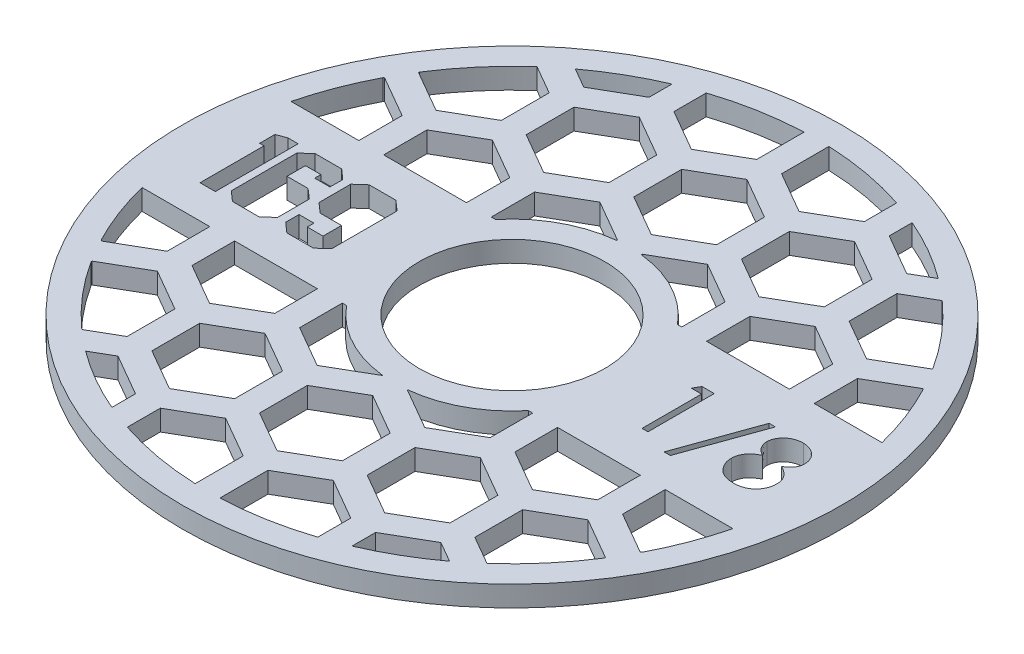
SolidWorks part; units mm, degrees
ref_plane "Front Plane" through (0, 0, 0) normal (0, 0, 1) x (1, 0, 0)
ref_plane "Top Plane" through (0, 0, 0) normal (0, 1, 0) x (1, 0, 0)
ref_plane "Right Plane" through (0, 0, 0) normal (1, 0, 0) x (0, 0, -1)
sketch "Sketch1" plane through (0, 0, 0) normal (0, 1, 0) x (1, 0, 0)
  circle A0 centre (0, 0) radius 14.224
  circle A1 centre (0, 0) radius 50.546
  dimension "D1" = 28.448
  dimension "D2" = 101.092
extrude "Boss-Extrude1" add sketch "Sketch1" along normal blind 3.175
sketch "Sketch2" plane through (0, 3.175, 0) normal (0, 1, 0) x (1, 0, 0)
  line L0 (-14.224, 0) -> (-50.546, 0) construction
  line L1 (-14.224, -6.35) -> (-50.546, -6.35) construction
  line L2 (14.224, 0) -> (50.546, 0) construction
  line L3 (14.224, -5.08) -> (50.546, -5.08) construction
  circle A0 centre (0, 0) radius 14.224 construction
  circle A1 centre (0, 0) radius 50.546 construction
  text T0 "169" font "Jersey M54" height 12.7
  text T1 "1/8" font "Century Gothic" height 10.16
  dimension "D1" = 6.35
  dimension "D2" = 5.08
extrude "Cut-Extrude1" cut sketch "Sketch2" against normal through all both and the other way through all
sketch "Sketch3" plane through (0, 3.175, 0) normal (0, 1, 0) x (1, 0, 0)
  line L0 (0, 11.43) -> (0, -11.43)
  line L1 (-49.2367, 11.43) -> (49.2367, 11.43)
  line L2 (-49.2367, -11.43) -> (49.2367, -11.43)
  line L3 (16.51, -7.3323) -> (22.86, -3.6662)
  line L4 (0, -7.3323) -> (6.35, -3.6662)
  line L5 (6.35, -3.6662) -> (6.35, 3.6662)
  line L6 (6.35, 3.6662) -> (0, 7.3323)
  line L7 (0, 7.3323) -> (-6.35, 3.6662)
  line L8 (-6.35, 3.6662) -> (-6.35, -3.6662)
  line L9 (-6.35, -3.6662) -> (0, -7.3323)
  line L16 (8.255, -21.6304) -> (14.605, -17.9643)
  line L17 (14.605, -17.9643) -> (14.605, -10.6319)
  line L18 (14.605, -10.6319) -> (8.255, -6.9657)
  line L19 (8.255, -6.9657) -> (1.905, -10.6319)
  line L20 (1.905, -10.6319) -> (1.905, -17.9643)
  line L21 (1.905, -17.9643) -> (8.255, -21.6304)
  line L22 (22.86, -3.6662) -> (22.86, 3.6662)
  line L23 (22.86, 3.6662) -> (16.51, 7.3323)
  line L24 (16.51, 7.3323) -> (10.16, 3.6662)
  line L25 (10.16, 3.6662) -> (10.16, -3.6662)
  line L26 (10.16, -3.6662) -> (16.51, -7.3323)
  line L27 (24.765, -21.6304) -> (31.115, -17.9643)
  line L28 (31.115, -17.9643) -> (31.115, -10.6319)
  line L29 (31.115, -10.6319) -> (24.765, -6.9657)
  line L30 (24.765, -6.9657) -> (18.415, -10.6319)
  line L31 (18.415, -10.6319) -> (18.415, -17.9643)
  line L32 (18.415, -17.9643) -> (24.765, -21.6304)
  line L33 (33.02, -7.3323) -> (39.37, -3.6662)
  line L34 (39.37, -3.6662) -> (39.37, 3.6662)
  line L35 (39.37, 3.6662) -> (33.02, 7.3323)
  line L36 (33.02, 7.3323) -> (26.67, 3.6662)
  line L37 (26.67, 3.6662) -> (26.67, -3.6662)
  line L38 (26.67, -3.6662) -> (33.02, -7.3323)
  line L39 (41.275, -21.6304) -> (47.625, -17.9643)
  line L40 (47.625, -17.9643) -> (47.625, -10.6319)
  line L41 (47.625, -10.6319) -> (41.275, -6.9657)
  line L42 (41.275, -6.9657) -> (34.925, -10.6319)
  line L43 (34.925, -10.6319) -> (34.925, -17.9643)
  line L44 (34.925, -17.9643) -> (41.275, -21.6304)
  line L45 (49.53, -7.3323) -> (55.88, -3.6662)
  line L46 (55.88, -3.6662) -> (55.88, 3.6662)
  line L47 (55.88, 3.6662) -> (49.53, 7.3323)
  line L48 (49.53, 7.3323) -> (43.18, 3.6662)
  line L49 (43.18, 3.6662) -> (43.18, -3.6662)
  line L50 (43.18, -3.6662) -> (49.53, -7.3323)
  line L51 (57.785, -21.6304) -> (64.135, -17.9643)
  line L52 (64.135, -17.9643) -> (64.135, -10.6319)
  line L53 (64.135, -10.6319) -> (57.785, -6.9657)
  line L54 (57.785, -6.9657) -> (51.435, -10.6319)
  line L55 (51.435, -10.6319) -> (51.435, -17.9643)
  line L56 (51.435, -17.9643) -> (57.785, -21.6304)
  line L57 (-16.51, -7.3323) -> (-10.16, -3.6662)
  line L58 (-10.16, -3.6662) -> (-10.16, 3.6662)
  line L59 (-10.16, 3.6662) -> (-16.51, 7.3323)
  line L60 (-16.51, 7.3323) -> (-22.86, 3.6662)
  line L61 (-22.86, 3.6662) -> (-22.86, -3.6662)
  line L62 (-22.86, -3.6662) -> (-16.51, -7.3323)
  line L63 (-8.255, -21.6304) -> (-1.905, -17.9643)
  line L64 (-1.905, -17.9643) -> (-1.905, -10.6319)
  line L65 (-1.905, -10.6319) -> (-8.255, -6.9657)
  line L66 (-8.255, -6.9657) -> (-14.605, -10.6319)
  line L67 (-14.605, -10.6319) -> (-14.605, -17.9643)
  line L68 (-14.605, -17.9643) -> (-8.255, -21.6304)
  line L69 (-33.02, -7.3323) -> (-26.67, -3.6662)
  line L70 (-26.67, -3.6662) -> (-26.67, 3.6662)
  line L71 (-26.67, 3.6662) -> (-33.02, 7.3323)
  line L72 (-33.02, 7.3323) -> (-39.37, 3.6662)
  line L73 (-39.37, 3.6662) -> (-39.37, -3.6662)
  line L74 (-39.37, -3.6662) -> (-33.02, -7.3323)
  line L75 (-24.765, -21.6304) -> (-18.415, -17.9643)
  line L76 (-18.415, -17.9643) -> (-18.415, -10.6319)
  line L77 (-18.415, -10.6319) -> (-24.765, -6.9657)
  line L78 (-24.765, -6.9657) -> (-31.115, -10.6319)
  line L79 (-31.115, -10.6319) -> (-31.115, -17.9643)
  line L80 (-31.115, -17.9643) -> (-24.765, -21.6304)
  line L81 (-49.53, -7.3323) -> (-43.18, -3.6662)
  line L82 (-43.18, -3.6662) -> (-43.18, 3.6662)
  line L83 (-43.18, 3.6662) -> (-49.53, 7.3323)
  line L84 (-49.53, 7.3323) -> (-55.88, 3.6662)
  line L85 (-55.88, 3.6662) -> (-55.88, -3.6662)
  line L86 (-55.88, -3.6662) -> (-49.53, -7.3323)
  line L87 (-41.275, -21.6304) -> (-34.925, -17.9643)
  line L88 (-34.925, -17.9643) -> (-34.925, -10.6319)
  line L89 (-34.925, -10.6319) -> (-41.275, -6.9657)
  line L90 (-41.275, -6.9657) -> (-47.625, -10.6319)
  line L91 (-47.625, -10.6319) -> (-47.625, -17.9643)
  line L92 (-47.625, -17.9643) -> (-41.275, -21.6304)
  line L93 (-49.53, 21.3697) -> (-43.18, 25.0358)
  line L94 (-43.18, 25.0358) -> (-43.18, 32.3682)
  line L95 (-43.18, 32.3682) -> (-49.53, 36.0343)
  line L96 (-49.53, 36.0343) -> (-55.88, 32.3682)
  line L97 (-55.88, 32.3682) -> (-55.88, 25.0358)
  line L98 (-55.88, 25.0358) -> (-49.53, 21.3697)
  line L99 (-41.275, 7.0716) -> (-34.925, 10.7377)
  line L100 (-34.925, 10.7377) -> (-34.925, 18.0701)
  line L101 (-34.925, 18.0701) -> (-41.275, 21.7363)
  line L102 (-41.275, 21.7363) -> (-47.625, 18.0701)
  line L103 (-47.625, 18.0701) -> (-47.625, 10.7377)
  line L104 (-47.625, 10.7377) -> (-41.275, 7.0716)
  line L105 (-33.02, 21.3697) -> (-26.67, 25.0358)
  line L106 (-26.67, 25.0358) -> (-26.67, 32.3682)
  line L107 (-26.67, 32.3682) -> (-33.02, 36.0343)
  line L108 (-33.02, 36.0343) -> (-39.37, 32.3682)
  line L109 (-39.37, 32.3682) -> (-39.37, 25.0358)
  line L110 (-39.37, 25.0358) -> (-33.02, 21.3697)
  line L111 (-24.765, 7.0716) -> (-18.415, 10.7377)
  line L112 (-18.415, 10.7377) -> (-18.415, 18.0701)
  line L113 (-18.415, 18.0701) -> (-24.765, 21.7363)
  line L114 (-24.765, 21.7363) -> (-31.115, 18.0701)
  line L115 (-31.115, 18.0701) -> (-31.115, 10.7377)
  line L116 (-31.115, 10.7377) -> (-24.765, 7.0716)
  line L117 (-16.51, 21.3697) -> (-10.16, 25.0358)
  line L118 (-10.16, 25.0358) -> (-10.16, 32.3682)
  line L119 (-10.16, 32.3682) -> (-16.51, 36.0343)
  line L120 (-16.51, 36.0343) -> (-22.86, 32.3682)
  line L121 (-22.86, 32.3682) -> (-22.86, 25.0358)
  line L122 (-22.86, 25.0358) -> (-16.51, 21.3697)
  line L123 (-8.255, 7.0716) -> (-1.905, 10.7377)
  line L124 (-1.905, 10.7377) -> (-1.905, 18.0701)
  line L125 (-1.905, 18.0701) -> (-8.255, 21.7363)
  line L126 (-8.255, 21.7363) -> (-14.605, 18.0701)
  line L127 (-14.605, 18.0701) -> (-14.605, 10.7377)
  line L128 (-14.605, 10.7377) -> (-8.255, 7.0716)
  line L129 (0, 21.3697) -> (6.35, 25.0358)
  line L130 (6.35, 25.0358) -> (6.35, 32.3682)
  line L131 (6.35, 32.3682) -> (0, 36.0343)
  line L132 (0, 36.0343) -> (-6.35, 32.3682)
  line L133 (-6.35, 32.3682) -> (-6.35, 25.0358)
  line L134 (-6.35, 25.0358) -> (0, 21.3697)
  line L135 (8.255, 7.0716) -> (14.605, 10.7377)
  line L136 (14.605, 10.7377) -> (14.605, 18.0701)
  line L137 (14.605, 18.0701) -> (8.255, 21.7363)
  line L138 (8.255, 21.7363) -> (1.905, 18.0701)
  line L139 (1.905, 18.0701) -> (1.905, 10.7377)
  line L140 (1.905, 10.7377) -> (8.255, 7.0716)
  line L141 (16.51, 21.3697) -> (22.86, 25.0358)
  line L142 (22.86, 25.0358) -> (22.86, 32.3682)
  line L143 (22.86, 32.3682) -> (16.51, 36.0343)
  line L144 (16.51, 36.0343) -> (10.16, 32.3682)
  line L145 (10.16, 32.3682) -> (10.16, 25.0358)
  line L146 (10.16, 25.0358) -> (16.51, 21.3697)
  line L147 (24.765, 7.0716) -> (31.115, 10.7377)
  line L148 (31.115, 10.7377) -> (31.115, 18.0701)
  line L149 (31.115, 18.0701) -> (24.765, 21.7363)
  line L150 (24.765, 21.7363) -> (18.415, 18.0701)
  line L151 (18.415, 18.0701) -> (18.415, 10.7377)
  line L152 (18.415, 10.7377) -> (24.765, 7.0716)
  line L153 (33.02, 21.3697) -> (39.37, 25.0358)
  line L154 (39.37, 25.0358) -> (39.37, 32.3682)
  line L155 (39.37, 32.3682) -> (33.02, 36.0343)
  line L156 (33.02, 36.0343) -> (26.67, 32.3682)
  line L157 (26.67, 32.3682) -> (26.67, 25.0358)
  line L158 (26.67, 25.0358) -> (33.02, 21.3697)
  line L159 (41.275, 7.0716) -> (47.625, 10.7377)
  line L160 (47.625, 10.7377) -> (47.625, 18.0701)
  line L161 (47.625, 18.0701) -> (41.275, 21.7363)
  line L162 (41.275, 21.7363) -> (34.925, 18.0701)
  line L163 (34.925, 18.0701) -> (34.925, 10.7377)
  line L164 (34.925, 10.7377) -> (41.275, 7.0716)
  line L165 (49.53, 21.3697) -> (55.88, 25.0358)
  line L166 (55.88, 25.0358) -> (55.88, 32.3682)
  line L167 (55.88, 32.3682) -> (49.53, 36.0343)
  line L168 (49.53, 36.0343) -> (43.18, 32.3682)
  line L169 (43.18, 32.3682) -> (43.18, 25.0358)
  line L170 (43.18, 25.0358) -> (49.53, 21.3697)
  line L171 (57.785, 7.0716) -> (64.135, 10.7377)
  line L172 (64.135, 10.7377) -> (64.135, 18.0701)
  line L173 (64.135, 18.0701) -> (57.785, 21.7363)
  line L174 (57.785, 21.7363) -> (51.435, 18.0701)
  line L175 (51.435, 18.0701) -> (51.435, 10.7377)
  line L176 (51.435, 10.7377) -> (57.785, 7.0716)
  line L177 (-49.53, 50.0717) -> (-43.18, 53.7378)
  line L178 (-43.18, 53.7378) -> (-43.18, 61.0702)
  line L179 (-43.18, 61.0702) -> (-49.53, 64.7363)
  line L180 (-49.53, 64.7363) -> (-55.88, 61.0702)
  line L181 (-55.88, 61.0702) -> (-55.88, 53.7378)
  line L182 (-55.88, 53.7378) -> (-49.53, 50.0717)
  line L183 (-41.275, 35.7736) -> (-34.925, 39.4397)
  line L184 (-34.925, 39.4397) -> (-34.925, 46.7721)
  line L185 (-34.925, 46.7721) -> (-41.275, 50.4383)
  line L186 (-41.275, 50.4383) -> (-47.625, 46.7721)
  line L187 (-47.625, 46.7721) -> (-47.625, 39.4397)
  line L188 (-47.625, 39.4397) -> (-41.275, 35.7736)
  line L189 (-33.02, 50.0717) -> (-26.67, 53.7378)
  line L190 (-26.67, 53.7378) -> (-26.67, 61.0702)
  line L191 (-26.67, 61.0702) -> (-33.02, 64.7363)
  line L192 (-33.02, 64.7363) -> (-39.37, 61.0702)
  line L193 (-39.37, 61.0702) -> (-39.37, 53.7378)
  line L194 (-39.37, 53.7378) -> (-33.02, 50.0717)
  line L195 (-24.765, 35.7736) -> (-18.415, 39.4397)
  line L196 (-18.415, 39.4397) -> (-18.415, 46.7721)
  line L197 (-18.415, 46.7721) -> (-24.765, 50.4383)
  line L198 (-24.765, 50.4383) -> (-31.115, 46.7721)
  line L199 (-31.115, 46.7721) -> (-31.115, 39.4397)
  line L200 (-31.115, 39.4397) -> (-24.765, 35.7736)
  line L201 (-16.51, 50.0717) -> (-10.16, 53.7378)
  line L202 (-10.16, 53.7378) -> (-10.16, 61.0702)
  line L203 (-10.16, 61.0702) -> (-16.51, 64.7363)
  line L204 (-16.51, 64.7363) -> (-22.86, 61.0702)
  line L205 (-22.86, 61.0702) -> (-22.86, 53.7378)
  line L206 (-22.86, 53.7378) -> (-16.51, 50.0717)
  line L207 (-8.255, 35.7736) -> (-1.905, 39.4397)
  line L208 (-1.905, 39.4397) -> (-1.905, 46.7721)
  line L209 (-1.905, 46.7721) -> (-8.255, 50.4383)
  line L210 (-8.255, 50.4383) -> (-14.605, 46.7721)
  line L211 (-14.605, 46.7721) -> (-14.605, 39.4397)
  line L212 (-14.605, 39.4397) -> (-8.255, 35.7736)
  line L213 (0, 50.0717) -> (6.35, 53.7378)
  line L214 (6.35, 53.7378) -> (6.35, 61.0702)
  line L215 (6.35, 61.0702) -> (0, 64.7363)
  line L216 (0, 64.7363) -> (-6.35, 61.0702)
  line L217 (-6.35, 61.0702) -> (-6.35, 53.7378)
  line L218 (-6.35, 53.7378) -> (0, 50.0717)
  line L219 (8.255, 35.7736) -> (14.605, 39.4397)
  line L220 (14.605, 39.4397) -> (14.605, 46.7721)
  line L221 (14.605, 46.7721) -> (8.255, 50.4383)
  line L222 (8.255, 50.4383) -> (1.905, 46.7721)
  line L223 (1.905, 46.7721) -> (1.905, 39.4397)
  line L224 (1.905, 39.4397) -> (8.255, 35.7736)
  line L225 (16.51, 50.0717) -> (22.86, 53.7378)
  line L226 (22.86, 53.7378) -> (22.86, 61.0702)
  line L227 (22.86, 61.0702) -> (16.51, 64.7363)
  line L228 (16.51, 64.7363) -> (10.16, 61.0702)
  line L229 (10.16, 61.0702) -> (10.16, 53.7378)
  line L230 (10.16, 53.7378) -> (16.51, 50.0717)
  line L231 (24.765, 35.7736) -> (31.115, 39.4397)
  line L232 (31.115, 39.4397) -> (31.115, 46.7721)
  line L233 (31.115, 46.7721) -> (24.765, 50.4383)
  line L234 (24.765, 50.4383) -> (18.415, 46.7721)
  line L235 (18.415, 46.7721) -> (18.415, 39.4397)
  line L236 (18.415, 39.4397) -> (24.765, 35.7736)
  line L237 (33.02, 50.0717) -> (39.37, 53.7378)
  line L238 (39.37, 53.7378) -> (39.37, 61.0702)
  line L239 (39.37, 61.0702) -> (33.02, 64.7363)
  line L240 (33.02, 64.7363) -> (26.67, 61.0702)
  line L241 (26.67, 61.0702) -> (26.67, 53.7378)
  line L242 (26.67, 53.7378) -> (33.02, 50.0717)
  line L243 (41.275, 35.7736) -> (47.625, 39.4397)
  line L244 (47.625, 39.4397) -> (47.625, 46.7721)
  line L245 (47.625, 46.7721) -> (41.275, 50.4383)
  line L246 (41.275, 50.4383) -> (34.925, 46.7721)
  line L247 (34.925, 46.7721) -> (34.925, 39.4397)
  line L248 (34.925, 39.4397) -> (41.275, 35.7736)
  line L249 (49.53, 50.0717) -> (55.88, 53.7378)
  line L250 (55.88, 53.7378) -> (55.88, 61.0702)
  line L251 (55.88, 61.0702) -> (49.53, 64.7363)
  line L252 (49.53, 64.7363) -> (43.18, 61.0702)
  line L253 (43.18, 61.0702) -> (43.18, 53.7378)
  line L254 (43.18, 53.7378) -> (49.53, 50.0717)
  line L255 (57.785, 35.7736) -> (64.135, 39.4397)
  line L256 (64.135, 39.4397) -> (64.135, 46.7721)
  line L257 (64.135, 46.7721) -> (57.785, 50.4383)
  line L258 (57.785, 50.4383) -> (51.435, 46.7721)
  line L259 (51.435, 46.7721) -> (51.435, 39.4397)
  line L260 (51.435, 39.4397) -> (57.785, 35.7736)
  line L261 (-49.53, -36.0343) -> (-43.18, -32.3682)
  line L262 (-43.18, -32.3682) -> (-43.18, -25.0358)
  line L263 (-43.18, -25.0358) -> (-49.53, -21.3697)
  line L264 (-49.53, -21.3697) -> (-55.88, -25.0358)
  line L265 (-55.88, -25.0358) -> (-55.88, -32.3682)
  line L266 (-55.88, -32.3682) -> (-49.53, -36.0343)
  line L267 (-41.275, -50.3324) -> (-34.925, -46.6663)
  line L268 (-34.925, -46.6663) -> (-34.925, -39.3339)
  line L269 (-34.925, -39.3339) -> (-41.275, -35.6677)
  line L270 (-41.275, -35.6677) -> (-47.625, -39.3339)
  line L271 (-47.625, -39.3339) -> (-47.625, -46.6663)
  line L272 (-47.625, -46.6663) -> (-41.275, -50.3324)
  line L273 (-33.02, -36.0343) -> (-26.67, -32.3682)
  line L274 (-26.67, -32.3682) -> (-26.67, -25.0358)
  line L275 (-26.67, -25.0358) -> (-33.02, -21.3697)
  line L276 (-33.02, -21.3697) -> (-39.37, -25.0358)
  line L277 (-39.37, -25.0358) -> (-39.37, -32.3682)
  line L278 (-39.37, -32.3682) -> (-33.02, -36.0343)
  line L279 (-24.765, -50.3324) -> (-18.415, -46.6663)
  line L280 (-18.415, -46.6663) -> (-18.415, -39.3339)
  line L281 (-18.415, -39.3339) -> (-24.765, -35.6677)
  line L282 (-24.765, -35.6677) -> (-31.115, -39.3339)
  line L283 (-31.115, -39.3339) -> (-31.115, -46.6663)
  line L284 (-31.115, -46.6663) -> (-24.765, -50.3324)
  line L285 (-16.51, -36.0343) -> (-10.16, -32.3682)
  line L286 (-10.16, -32.3682) -> (-10.16, -25.0358)
  line L287 (-10.16, -25.0358) -> (-16.51, -21.3697)
  line L288 (-16.51, -21.3697) -> (-22.86, -25.0358)
  line L289 (-22.86, -25.0358) -> (-22.86, -32.3682)
  line L290 (-22.86, -32.3682) -> (-16.51, -36.0343)
  line L291 (-8.255, -50.3324) -> (-1.905, -46.6663)
  line L292 (-1.905, -46.6663) -> (-1.905, -39.3339)
  line L293 (-1.905, -39.3339) -> (-8.255, -35.6677)
  line L294 (-8.255, -35.6677) -> (-14.605, -39.3339)
  line L295 (-14.605, -39.3339) -> (-14.605, -46.6663)
  line L296 (-14.605, -46.6663) -> (-8.255, -50.3324)
  line L297 (0, -36.0343) -> (6.35, -32.3682)
  line L298 (6.35, -32.3682) -> (6.35, -25.0358)
  line L299 (6.35, -25.0358) -> (0, -21.3697)
  line L300 (0, -21.3697) -> (-6.35, -25.0358)
  line L301 (-6.35, -25.0358) -> (-6.35, -32.3682)
  line L302 (-6.35, -32.3682) -> (0, -36.0343)
  line L303 (8.255, -50.3324) -> (14.605, -46.6663)
  line L304 (14.605, -46.6663) -> (14.605, -39.3339)
  line L305 (14.605, -39.3339) -> (8.255, -35.6677)
  line L306 (8.255, -35.6677) -> (1.905, -39.3339)
  line L307 (1.905, -39.3339) -> (1.905, -46.6663)
  line L308 (1.905, -46.6663) -> (8.255, -50.3324)
  line L309 (16.51, -36.0343) -> (22.86, -32.3682)
  line L310 (22.86, -32.3682) -> (22.86, -25.0358)
  line L311 (22.86, -25.0358) -> (16.51, -21.3697)
  line L312 (16.51, -21.3697) -> (10.16, -25.0358)
  line L313 (10.16, -25.0358) -> (10.16, -32.3682)
  line L314 (10.16, -32.3682) -> (16.51, -36.0343)
  line L315 (24.765, -50.3324) -> (31.115, -46.6663)
  line L316 (31.115, -46.6663) -> (31.115, -39.3339)
  line L317 (31.115, -39.3339) -> (24.765, -35.6677)
  line L318 (24.765, -35.6677) -> (18.415, -39.3339)
  line L319 (18.415, -39.3339) -> (18.415, -46.6663)
  line L320 (18.415, -46.6663) -> (24.765, -50.3324)
  line L321 (33.02, -36.0343) -> (39.37, -32.3682)
  line L322 (39.37, -32.3682) -> (39.37, -25.0358)
  line L323 (39.37, -25.0358) -> (33.02, -21.3697)
  line L324 (33.02, -21.3697) -> (26.67, -25.0358)
  line L325 (26.67, -25.0358) -> (26.67, -32.3682)
  line L326 (26.67, -32.3682) -> (33.02, -36.0343)
  line L327 (41.275, -50.3324) -> (47.625, -46.6663)
  line L328 (47.625, -46.6663) -> (47.625, -39.3339)
  line L329 (47.625, -39.3339) -> (41.275, -35.6677)
  line L330 (41.275, -35.6677) -> (34.925, -39.3339)
  line L331 (34.925, -39.3339) -> (34.925, -46.6663)
  line L332 (34.925, -46.6663) -> (41.275, -50.3324)
  line L333 (49.53, -36.0343) -> (55.88, -32.3682)
  line L334 (55.88, -32.3682) -> (55.88, -25.0358)
  line L335 (55.88, -25.0358) -> (49.53, -21.3697)
  line L336 (49.53, -21.3697) -> (43.18, -25.0358)
  line L337 (43.18, -25.0358) -> (43.18, -32.3682)
  line L338 (43.18, -32.3682) -> (49.53, -36.0343)
  line L339 (57.785, -50.3324) -> (64.135, -46.6663)
  line L340 (64.135, -46.6663) -> (64.135, -39.3339)
  line L341 (64.135, -39.3339) -> (57.785, -35.6677)
  line L342 (57.785, -35.6677) -> (51.435, -39.3339)
  line L343 (51.435, -39.3339) -> (51.435, -46.6663)
  line L344 (51.435, -46.6663) -> (57.785, -50.3324)
  circle A0 centre (0, 0) radius 50.546 construction
  circle A1 centre (0, 0) radius 18.034
  circle A2 centre (0, 0) radius 46.736
  circle A3 centre (0, 0) radius 6.35 construction
  circle A4 centre (8.255, -14.2981) radius 6.35 construction
  point P4 (0, 0)
  point P10 (0, 11.43)
  point P13 (0, -11.43)
  dimension "D2" = 36.068
  dimension "D3" = 93.472
  dimension "D1" = 22.86
  dimension "D4" = 12.7
  dimension "D5" = 12.7
  dimension "D6" = 3.81
  dimension "D7" = 1.905
  dimension "D8" = 4
  dimension "D9" = 4
  dimension "D10" = 3
  dimension "D11" = 2
extrude "Cut-Extrude2" cut sketch "Sketch3" against normal through all both and the other way through all contours L102 A2 L1 L100 L101 | L114 L115 L1 L112 L113 | L107 A2 L109 L110 L105 L106 | L196 A2 L200 L195 | L121 L122 L117 L118 L119 L120 | L208 A2 L211 L212 L207 | L133 L134 L129 L130 L131 L132 | L220 A2 L223 L224 L219 | A1 L124 L125 L126 L127 L1 | A1 L1 L136 L137 L138 L139 | L145 L146 L141 L142 L143 L144 | L231 A2 L235 L236 | L154 A2 L156 L157 L158 L153 | L150 L151 L1 L148 L149 | L1 A2 L161 L162 L163 | L39 A2 L2 L43 L44 | L31 L32 L27 L28 L2 | L326 A2 L322 L323 L324 L325 | L313 L314 L309 L310 L311 L312 | A1 L20 L21 L16 L17 L2 | L301 L302 L297 L298 L299 L300 | L319 A2 L317 L318 | L308 A2 L304 L305 L306 L307 | L295 A2 L291 L292 L293 L294 | L282 A2 L280 L281 | L289 L290 L285 L286 L287 L288 | L277 A2 L273 L274 L275 L276 | L2 A2 L92 L87 L88 | L79 L80 L75 L76 L2 | A1 L2 L67 L68 L63 L64
